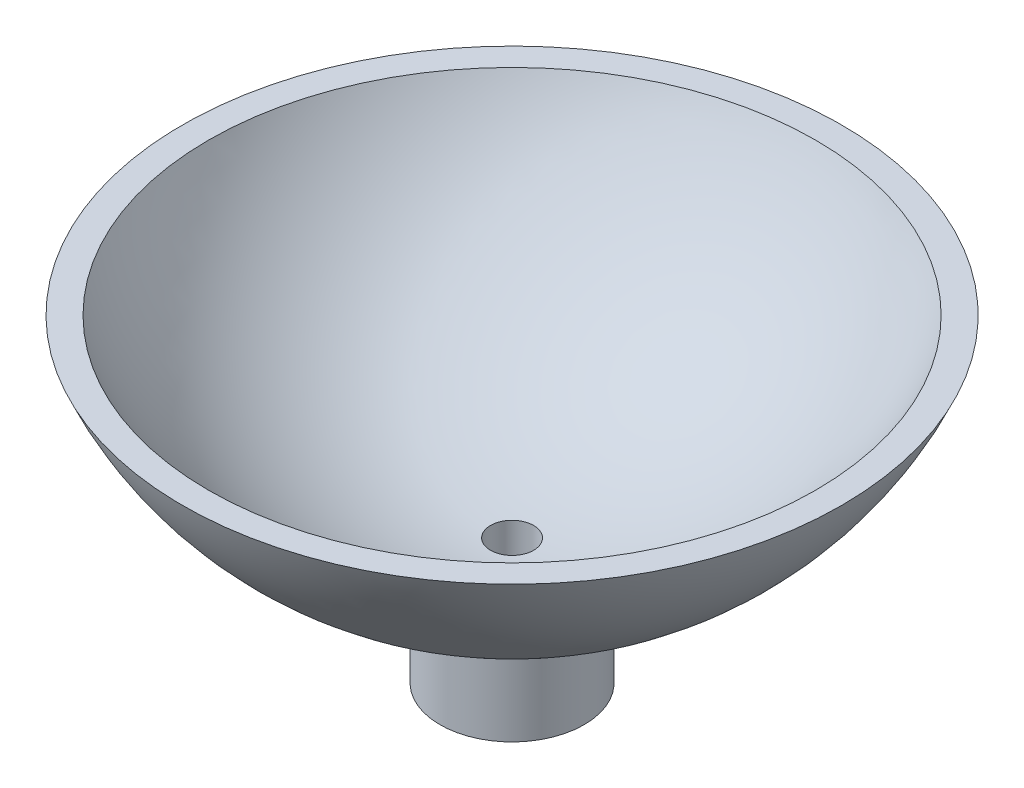
SolidWorks part; units mm, degrees
ref_plane "Front Plane" through (0, 0, 0) normal (0, 0, 1) x (1, 0, 0)
ref_plane "Top Plane" through (0, 0, 0) normal (0, 1, 0) x (1, 0, 0)
ref_plane "Right Plane" through (0, 0, 0) normal (1, 0, 0) x (0, 0, -1)
sketch "Sketch5" plane through (0, 0, 0) normal (0, 0, 1) x (1, 0, 0)
  line L0 (0, -22.5) -> (0, -28.85) construction
  line L1 (0, -28.85) -> (-1.3525, -28.85) construction
  line L2 (-1.3525, -28.85) -> (-1.3525, -22.4593)
  line L3 (-1.3525, -28.85) -> (-4.5275, -28.85)
  line L4 (-4.5275, -28.85) -> (-4.5275, -22.0398)
  line L5 (-1.3525, -22.4593) -> (-1.3525, -20.9564)
  line L7 (-20.6864, -8.85) -> (-19.0441, -8.85)
  line L8 (0, -28.85) -> (0, 0) construction
  circle A0 centre (0, 0) radius 22.5 construction
  circle A1 centre (0, 0) radius 21 construction
  arc A2 (-19.0441, -8.85) -> (-1.3525, -20.9564) centre (0, 0) ccw
  arc A3 (-20.6864, -8.85) -> (-4.5275, -22.0398) centre (0, 0) ccw
  dimension "D1" = 45
  dimension "D5" = 42
  dimension "D2" = 6.35
  dimension "D3" = 1.3525
  dimension "D4" = 3.175
  dimension "D6" = 20
revolve "Revolve2" add sketch "Sketch5" angle 360 about L8
